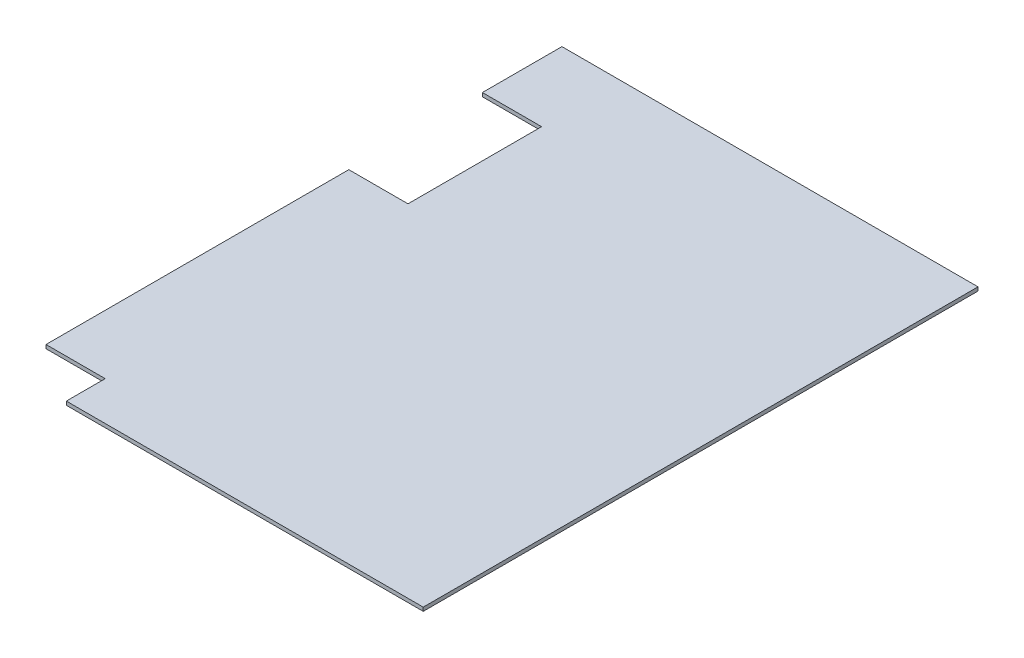
SolidWorks part; units mm, degrees
ref_plane "Front Plane" through (0, 0, 0) normal (0, 0, 1) x (1, 0, 0)
ref_plane "Top Plane" through (0, 0, 0) normal (0, 1, 0) x (1, 0, 0)
ref_plane "Right Plane" through (0, 0, 0) normal (1, 0, 0) x (0, 0, -1)
sketch "Sketch1" plane through (0, 0, 0) normal (0, 1, 0) x (1, 0, 0)
  line L0 (-2857.5, 882.65) -> (-2857.5, 2717.8)
  line L1 (2857.5, -3810) -> (-2044.7, -3810)
  line L2 (2857.5, -3810) -> (2857.5, 3810)
  line L3 (2857.5, 3810) -> (-2857.5, 3810)
  line L4 (-2857.5, -3276.6) -> (-2857.5, 3810)
  line L5 (2857.5, -3810) -> (-2857.5, 3810) construction
  line L6 (2857.5, 3810) -> (-2457.45, -3276.6) construction
  line L7 (-2857.5, 882.65) -> (-2044.7, 882.65)
  line L8 (-2857.5, 2717.8) -> (-2044.7, 2717.8)
  line L9 (-2044.7, 882.65) -> (-2044.7, 2717.8)
  line L13 (-2857.5, -3276.6) -> (-2044.7, -3276.6)
  line L14 (-2044.7, -3810) -> (-2044.7, -3276.6)
  point P0 (0, 0)
  dimension "D2" = 5715
  dimension "D3" = 1092.2
  dimension "D4" = 812.8
  dimension "D5" = 1835.15
  dimension "D6" = 533.4
  dimension "D7" = 812.8
extrude "Boss-Extrude2" add sketch "Sketch1" along normal blind 50.8 contours L9 L7 L4 L1 L2 L3 L8
